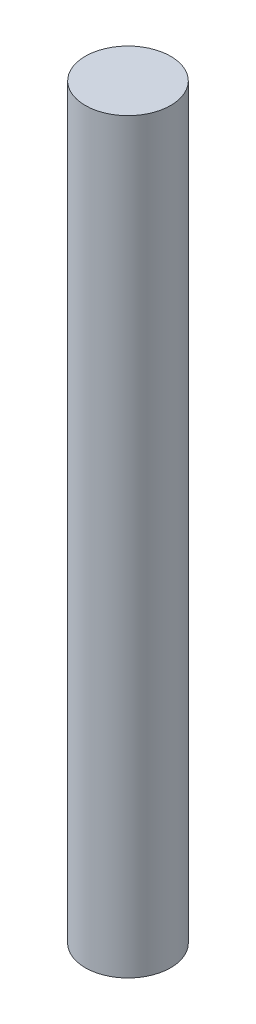
SolidWorks part; units mm, degrees
ref_plane "Front" through (0, 0, 0) normal (0, 0, 1) x (1, 0, 0)
ref_plane "Top" through (0, 0, 0) normal (0, 1, 0) x (1, 0, 0)
ref_plane "Right" through (0, 0, 0) normal (1, 0, 0) x (0, 0, -1)
sketch "草图1" plane through (0, 0, 0) normal (0, 1, 0) x (1, 0, 0)
  circle A0 centre (0, 0) radius 4
  dimension "D1" = 8
extrude "凸台-拉伸1" add sketch "草图1" along normal blind 70
